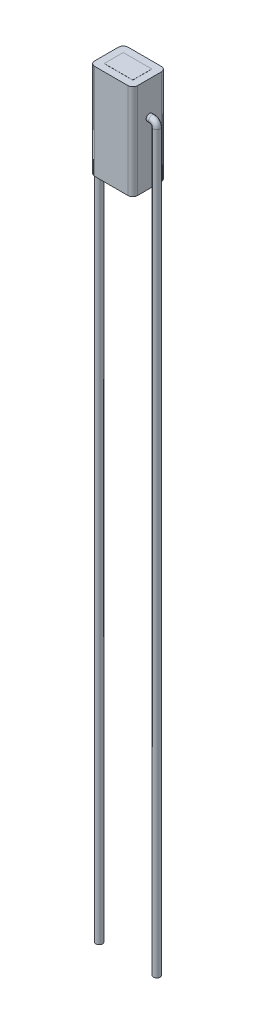
SolidWorks part; units mm, degrees
ref_plane "Front Plane" through (0, 0, 0) normal (0, 0, 1) x (1, 0, 0)
ref_plane "Top Plane" through (0, 0, 0) normal (0, 1, 0) x (1, 0, 0)
ref_plane "Right Plane" through (0, 0, 0) normal (1, 0, 0) x (0, 0, -1)
sketch "Sketch1" plane through (0, 0, 0) normal (0, 1, 0) x (1, 0, 0)
  line L1 (-2.25, 1.75) -> (2.25, 1.75)
  line L2 (-2.25, 1.75) -> (-2.25, -1.75)
  line L3 (-2.25, -1.75) -> (2.25, -1.75)
  line L4 (2.25, 1.75) -> (2.25, -1.75)
  line L5 (-2.25, 1.75) -> (2.25, -1.75) construction
  line L6 (-2.25, -1.75) -> (2.25, 1.75) construction
  point P0 (0, 0)
  dimension "D1" = 3.5
  dimension "D2" = 4.5
sketch "Sketch2" plane through (0, 0, 0) normal (0, 1, 0) x (1, 0, 0)
  line L1 (-1.5, 1) -> (1.5, 1)
  line L2 (-1.5, 1) -> (-1.5, -1)
  line L3 (-1.5, -1) -> (1.5, -1)
  line L4 (1.5, 1) -> (1.5, -1)
  line L5 (-1.5, 1) -> (1.5, -1) construction
  line L6 (-1.5, -1) -> (1.5, 1) construction
  point P0 (0, 0)
  dimension "D1" = 2
  dimension "D2" = 3
extrude "Boss-Extrude1" add sketch "Sketch1" along normal blind 10
extrude "Boss-Extrude2" add sketch "Sketch2" along normal blind 10.01 and the other way blind 0.01
fillet "Fillet2" radius 0.5 4 edges at (2.25, 5, 1.75) (-2.25, 5, 1.75) (-2.25, 5, -1.75) (2.25, 5, -1.75)
sketch "Sketch14" plane through (2.25, 0, 0) normal (1, 0, 0) x (0, 0, -1)
  line L0 (-1.25, 0) -> (1.25, 0) construction
  circle A0 centre (0, 6.5) radius 0.35
  dimension "D1" = 6.5
sketch "Sketch15" plane through (0, 0, 0) normal (0, 0, 1) x (1, 0, 0)
  line L0 (2.25, 6.5) -> (2.3, 6.5)
  line L1 (2.3, 6.5) -> (2.5259, 6.5)
  line L2 (3.0259, 6) -> (3.0259, -71.1462)
  arc A0 (2.5259, 6.5) -> (3.0259, 6) centre (2.5259, 6) cw
sweep "Sweep1" add profiles "Sketch14" path "Sketch15"
mirror "Mirror1" about plane through (0, 0, 0) normal (1, 0, 0) of "Sweep1"
